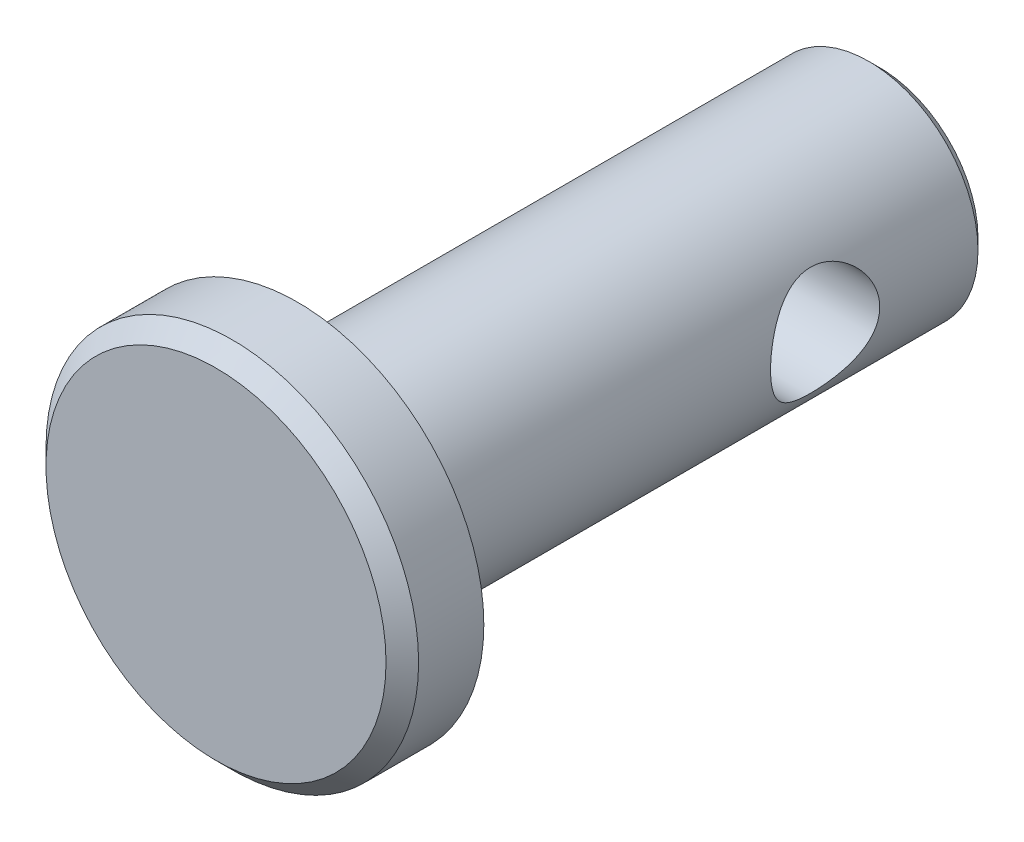
SolidWorks part; units mm, degrees
ref_plane "Front" through (0, 0, 0) normal (0, 0, 1) x (1, 0, 0)
ref_plane "Top" through (0, 0, 0) normal (0, 1, 0) x (1, 0, 0)
ref_plane "Right" through (0, 0, 0) normal (1, 0, 0) x (0, 0, -1)
sketch "Sketch1" plane through (0, 0, 0) normal (0, 0, 1) x (1, 0, 0)
  circle A0 centre (0, 0) radius 2.3812
  point P3 (0, 2.3812)
  point P4 (0, -2.3812)
  dimension "dia" = 4.7625
extrude "Extrude1" add sketch "Sketch1" along normal mid plane 12.7
sketch "Sketch2" plane through (0, 0, 6.35) normal (0, 0, 1) x (1, 0, 0)
  circle A0 centre (0, 0) radius 4.064
  dimension "head dia" = 8.128
extrude "Extrude2" add sketch "Sketch2" along normal blind 1.778
chamfer "Chamfer1" distance 0.3556 angle 45 1 edges at (4.064, 0, 8.128)
sketch "Sketch3" plane through (0, 0, 0) normal (1, 0, 0) x (0, 0, -1)
  line L0 (-6.35, -2.3812) -> (-6.35, 2.3812) construction
  circle A0 centre (2.7781, 0) radius 1.1906
  point P2 (1.5875, 0)
  dimension "hole dia" = 2.3813
  dimension "useable Lg" = 7.9375
extrude "Extrude3" cut sketch "Sketch3" against normal through all and the other way through all
chamfer "Chamfer2" distance 0.2381 angle 45 1 edges at (2.3812, 0, -6.35)
ref_plane "Plane1" through (0, 0, -2.7781) normal (0, 0, 1) x (1, 0, 0)
sketch "Sketch8" plane through (0, 0, 0) normal (1, 0, 0) x (0, 0, -1)
  line L0 (-8.128, 3.7084) -> (-8.128, -3.7084) construction
  line L1 (-7.7724, -4.064) -> (-6.35, -4.064) construction
  line L2 (6.35, -2.1431) -> (6.35, 2.1431) construction
  point P0 (-8.128, 4.064)
  point P1 (-6.35, 4.064)
  point P5 (6.35, 2.3812)
  point P8 (-8.128, -4.064)
  point P9 (6.35, -2.3812)
equation "\"D1@Chamfer1\" = \"head ht@Extrude2\" * .2"
equation "\"D1@Chamfer2\" = \"dia@Sketch1\" * .05"
